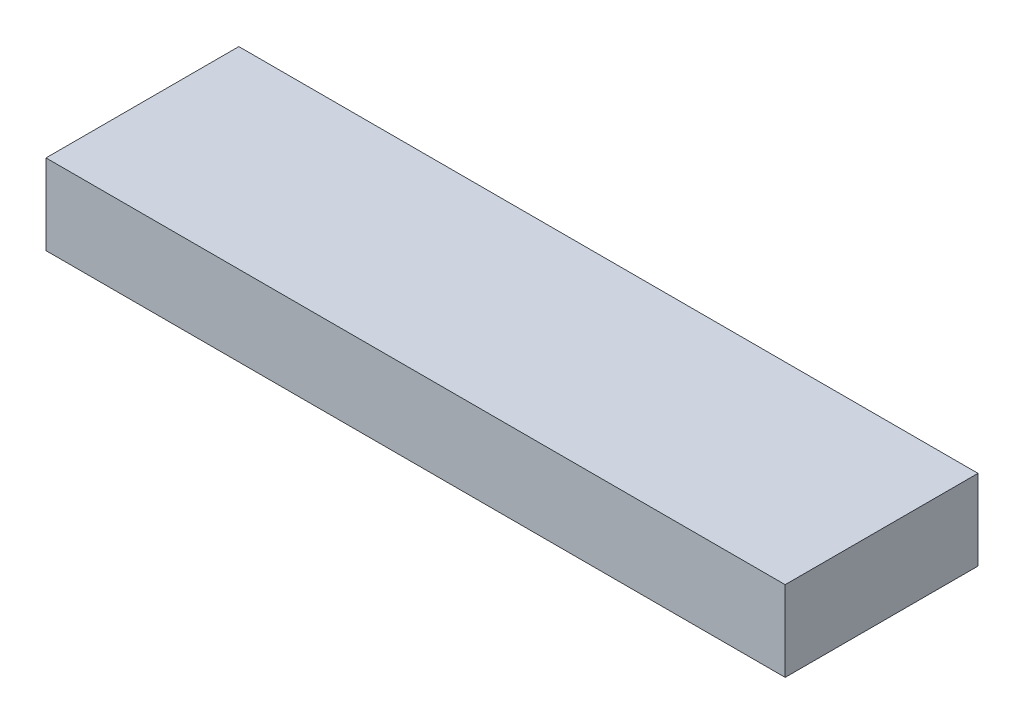
SolidWorks part; units mm, degrees
ref_plane "Front Plane" through (0, 0, 0) normal (0, 0, 1) x (1, 0, 0)
ref_plane "Top Plane" through (0, 0, 0) normal (0, 1, 0) x (1, 0, 0)
ref_plane "Right Plane" through (0, 0, 0) normal (1, 0, 0) x (0, 0, -1)
sketch "Sketch1" plane through (0, 0, 0) normal (0, 1, 0) x (1, 0, 0)
  line L1 (-14.6429, 10.5) -> (31.3571, 10.5)
  line L2 (-14.6429, 10.5) -> (-14.6429, -1.5)
  line L3 (-14.6429, -1.5) -> (31.3571, -1.5)
  line L4 (31.3571, 10.5) -> (31.3571, -1.5)
  dimension "D1" = 46
  dimension "D2" = 12
extrude "Boss-Extrude1" add sketch "Sketch1" along normal blind 5
